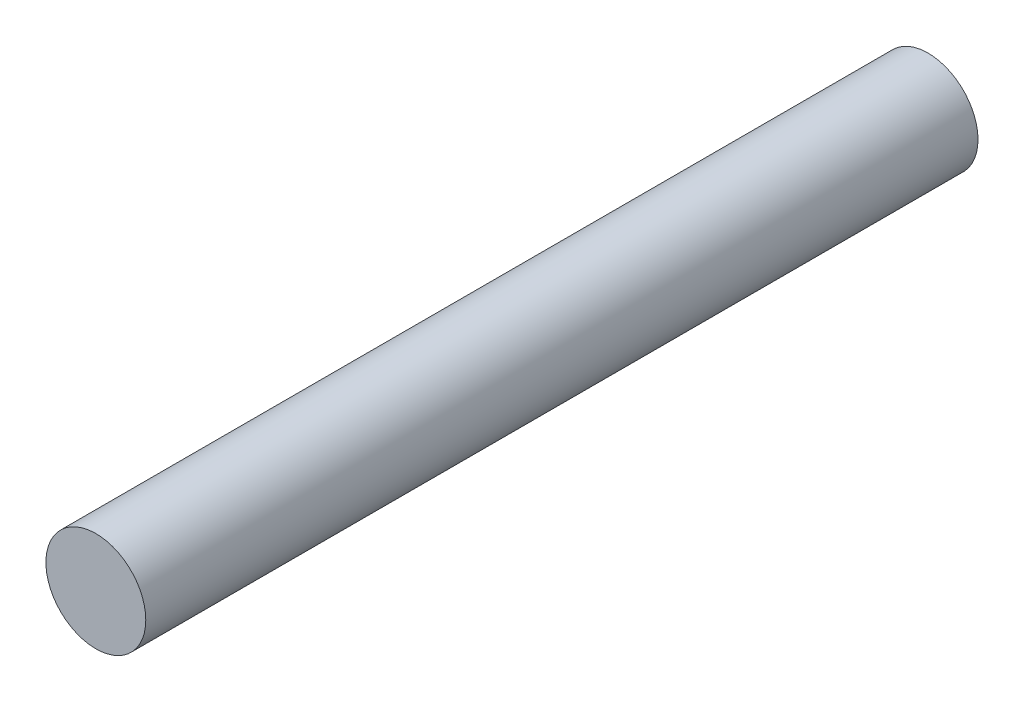
SolidWorks part; units mm, degrees
ref_plane "Front Plane" through (0, 0, 0) normal (0, 0, 1) x (1, 0, 0)
ref_plane "Top Plane" through (0, 0, 0) normal (0, 1, 0) x (1, 0, 0)
ref_plane "Right Plane" through (0, 0, 0) normal (1, 0, 0) x (0, 0, -1)
sketch "Sketch1" plane through (0, 0, 0) normal (0, 0, 1) x (1, 0, 0)
  circle A0 centre (0, 0) radius 1.5
extrude "Boss-Extrude1" add sketch "Sketch1" along normal blind 25 contours A0
